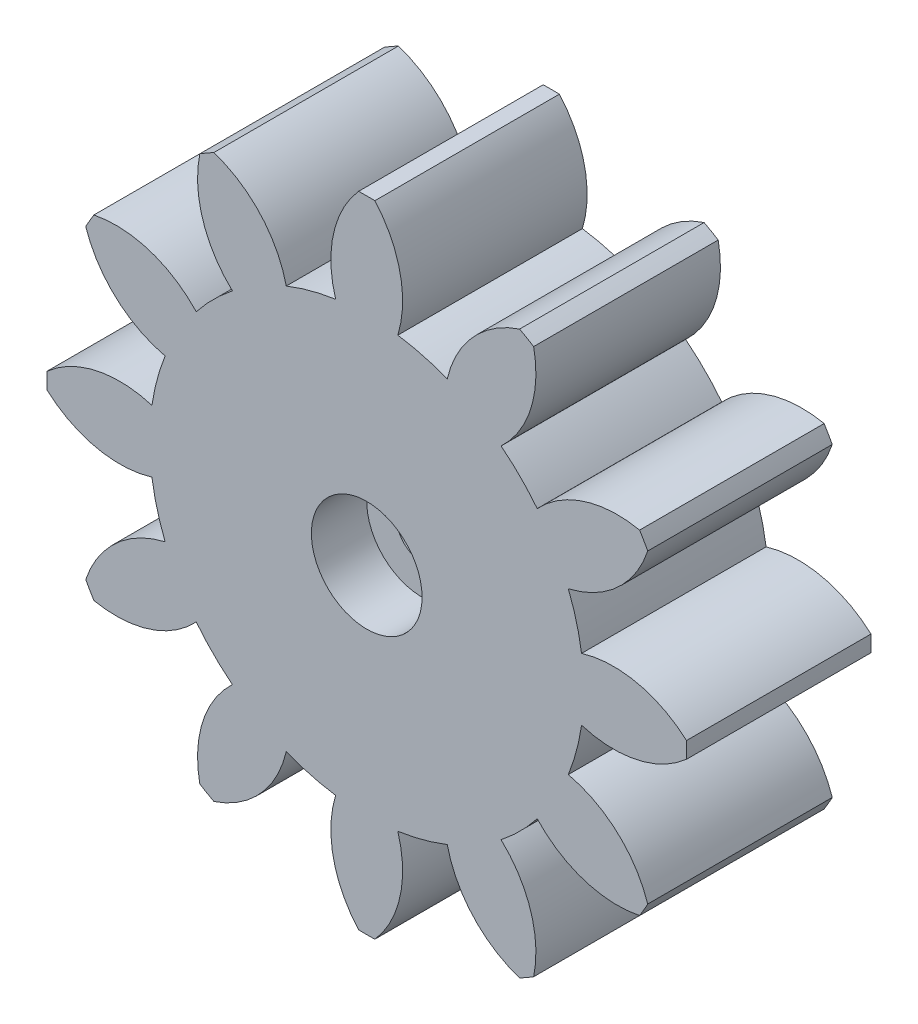
SolidWorks part; units mm, degrees
ref_plane "Front Plane" through (0, 0, 0) normal (0, 0, 1) x (1, 0, 0)
ref_plane "Top Plane" through (0, 0, 0) normal (0, 1, 0) x (1, 0, 0)
ref_plane "Right Plane" through (0, 0, 0) normal (1, 0, 0) x (0, 0, -1)
sketch "Sketch1" plane through (0, 0, 0) normal (0, 0, 1) x (1, 0, 0)
  arc A96 (10.9244, -4.3614) -> (11.6416, -1.6851) centre (0, 0) ccw
  arc A97 (11.6416, -1.6851) -> (17.3299, -0.4402) centre (13.3779, 3.9992) ccw
  arc A98 (17.3299, -0.4402) -> (17.3299, 0.4402) centre (0, 0) ccw
  arc A99 (17.3299, 0.4402) -> (11.6416, 1.6851) centre (13.3779, -3.9992) ccw
  arc A100 (11.6416, 1.6851) -> (10.9244, 4.3614) centre (0, 0) ccw
  arc A101 (10.9244, 4.3614) -> (15.2282, 8.2838) centre (9.586, 10.1524) ccw
  arc A102 (15.2282, 8.2838) -> (14.7881, 9.0462) centre (0, 0) ccw
  arc A103 (14.7881, 9.0462) -> (9.2393, 7.2801) centre (13.5852, 3.2255) ccw
  arc A104 (9.2393, 7.2801) -> (7.2801, 9.2393) centre (0, 0) ccw
  arc A105 (7.2801, 9.2393) -> (9.0462, 14.7881) centre (3.2255, 13.5852) ccw
  arc A106 (9.0462, 14.7881) -> (8.2838, 15.2282) centre (0, 0) ccw
  arc A107 (8.2838, 15.2282) -> (4.3614, 10.9244) centre (10.1524, 9.586) ccw
  arc A108 (4.3614, 10.9244) -> (1.6851, 11.6416) centre (0, 0) ccw
  arc A109 (1.6851, 11.6416) -> (0.4402, 17.3299) centre (-3.9992, 13.3779) ccw
  arc A110 (0.4402, 17.3299) -> (-0.4402, 17.3299) centre (0, 0) ccw
  arc A111 (-0.4402, 17.3299) -> (-1.6851, 11.6416) centre (3.9992, 13.3779) ccw
  arc A112 (-1.6851, 11.6416) -> (-4.3614, 10.9244) centre (0, 0) ccw
  arc A113 (-4.3614, 10.9244) -> (-8.2838, 15.2282) centre (-10.1524, 9.586) ccw
  arc A114 (-8.2838, 15.2282) -> (-9.0462, 14.7881) centre (0, 0) ccw
  arc A115 (-9.0462, 14.7881) -> (-7.2801, 9.2393) centre (-3.2255, 13.5852) ccw
  arc A116 (-7.2801, 9.2393) -> (-9.2393, 7.2801) centre (0, 0) ccw
  arc A117 (-9.2393, 7.2801) -> (-14.7881, 9.0462) centre (-13.5852, 3.2255) ccw
  arc A118 (-14.7881, 9.0462) -> (-15.2282, 8.2838) centre (0, 0) ccw
  arc A119 (-15.2282, 8.2838) -> (-10.9244, 4.3614) centre (-9.586, 10.1524) ccw
  arc A120 (-10.9244, 4.3614) -> (-11.6416, 1.6851) centre (0, 0) ccw
  arc A121 (-11.6416, 1.6851) -> (-17.3299, 0.4402) centre (-13.3779, -3.9992) ccw
  arc A122 (-17.3299, 0.4402) -> (-17.3299, -0.4402) centre (0, 0) ccw
  arc A123 (-17.3299, -0.4402) -> (-11.6416, -1.6851) centre (-13.3779, 3.9992) ccw
  arc A124 (-11.6416, -1.6851) -> (-10.9244, -4.3614) centre (0, 0) ccw
  arc A125 (-10.9244, -4.3614) -> (-15.2282, -8.2838) centre (-9.586, -10.1524) ccw
  arc A126 (-15.2282, -8.2838) -> (-14.7881, -9.0462) centre (0, 0) ccw
  arc A127 (-14.7881, -9.0462) -> (-9.2393, -7.2801) centre (-13.5852, -3.2255) ccw
  arc A128 (-9.2393, -7.2801) -> (-7.2801, -9.2393) centre (0, 0) ccw
  arc A129 (-7.2801, -9.2393) -> (-9.0462, -14.7881) centre (-3.2255, -13.5852) ccw
  arc A130 (-9.0462, -14.7881) -> (-8.2838, -15.2282) centre (0, 0) ccw
  arc A131 (-8.2838, -15.2282) -> (-4.3614, -10.9244) centre (-10.1524, -9.586) ccw
  arc A132 (-4.3614, -10.9244) -> (-1.6851, -11.6416) centre (0, 0) ccw
  arc A133 (-1.6851, -11.6416) -> (-0.4402, -17.3299) centre (3.9992, -13.3779) ccw
  arc A134 (-0.4402, -17.3299) -> (0.4402, -17.3299) centre (0, 0) ccw
  arc A135 (0.4402, -17.3299) -> (1.6851, -11.6416) centre (-3.9992, -13.3779) ccw
  arc A136 (1.6851, -11.6416) -> (4.3614, -10.9244) centre (0, 0) ccw
  arc A137 (4.3614, -10.9244) -> (8.2838, -15.2282) centre (10.1524, -9.586) ccw
  arc A138 (8.2838, -15.2282) -> (9.0462, -14.7881) centre (0, 0) ccw
  arc A139 (9.0462, -14.7881) -> (7.2801, -9.2393) centre (3.2255, -13.5852) ccw
  arc A140 (7.2801, -9.2393) -> (9.2393, -7.2801) centre (0, 0) ccw
  arc A141 (9.2393, -7.2801) -> (14.7881, -9.0462) centre (13.5852, -3.2255) ccw
  arc A142 (14.7881, -9.0462) -> (15.2282, -8.2838) centre (0, 0) ccw
  arc A143 (15.2282, -8.2838) -> (10.9244, -4.3614) centre (9.586, -10.1524) ccw
extrude "Boss-Extrude1" add sketch "Sketch1" along normal blind 10
sketch "Sketch3" plane through (0, 0, 10) normal (0, 0, 1) x (1, 0, 0)
  circle A0 centre (0, 0) radius 3
  dimension "D1" = 6
extrude "Cut-Extrude1" cut sketch "Sketch3" against normal blind 3
sketch "Sketch4" plane through (0, 0, 0) normal (0, 0, -1) x (-1, 0, 0)
  circle A0 centre (0, 0) radius 3 construction
  circle A1 centre (0, 0) radius 3
extrude "Cut-Extrude2" cut sketch "Sketch4" against normal offset from surface (5 mm away) 2 up to face at (3, 0, 7)
sketch "Sketch5" plane through (0, 0, 5) normal (0, 0, -1) x (-1, 0, 0)
  circle A0 centre (0, 0) radius 1.375
  dimension "D1" = 2.75
extrude "Cut-Extrude3" cut sketch "Sketch5" against normal up to next
sketch "Sketch6" plane through (0, 0, 0) normal (0, 0, -1) x (-1, 0, 0)
  text T0 "<i>Top</i>" font "Century Gothic" height in points 8
extrude "Cut-Extrude4" cut sketch "Sketch6" against normal blind 0.4
sketch "Sketch7" plane through (0, 0, 10) normal (0, 0, 1) x (1, 0, 0)
  point P0 (0, 0)
sketch "Sketch8" plane through (0, 0, 10) normal (0, 0, 1) x (1, 0, 0)
  line L0 (0, 0) -> (0, -17.3355) construction
  arc A0 (-0.4402, -17.3299) -> (0.4402, -17.3299) centre (0, 0) ccw construction
